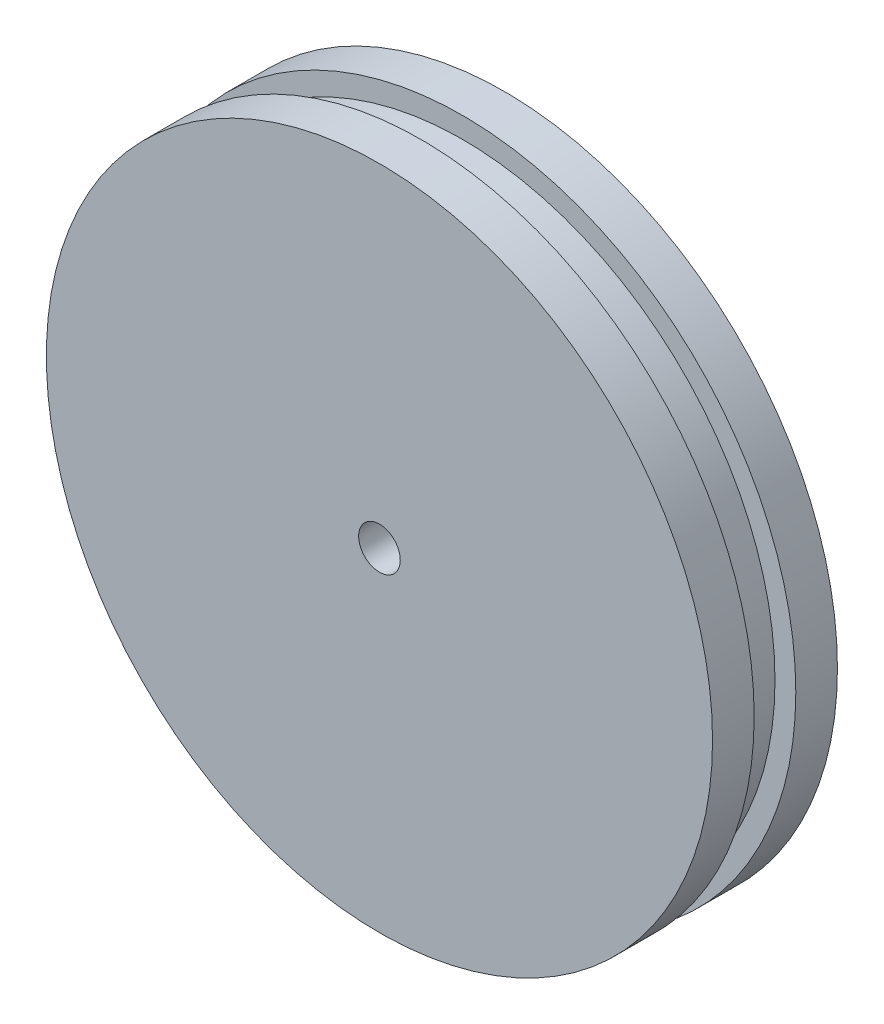
SolidWorks part; units mm, degrees
ref_plane "Alzado" through (0, 0, 0) normal (0, 0, 1) x (1, 0, 0)
ref_plane "Planta" through (0, 0, 0) normal (0, 1, 0) x (1, 0, 0)
ref_plane "Vista lateral" through (0, 0, 0) normal (1, 0, 0) x (0, 0, -1)
sketch "Croquis2" plane through (0, 0, 0) normal (0, 0, 1) x (1, 0, 0)
  circle A0 centre (0, 0) radius 56
  dimension "D1" = 112
extrude "Saliente-Extruir1" add sketch "Croquis2" along normal blind 7
sketch "Croquis3" plane through (0, 0, 7) normal (0, 0, 1) x (1, 0, 0)
  circle A0 centre (0, 0) radius 52.5
  dimension "D1" = 105
extrude "Saliente-Extruir2" add sketch "Croquis3" along normal blind 7
sketch "Croquis4" plane through (0, 0, 14) normal (0, 0, 1) x (1, 0, 0)
  circle A0 centre (0, 0) radius 56
  dimension "D1" = 112
extrude "Saliente-Extruir3" add sketch "Croquis4" along normal blind 7
sketch "Croquis5" plane through (0, 0, 21) normal (0, 0, 1) x (1, 0, 0)
  circle A0 centre (0, 0) radius 3.5
  dimension "D1" = 7
extrude "Cortar-Extruir1" cut sketch "Croquis5" against normal blind 77
